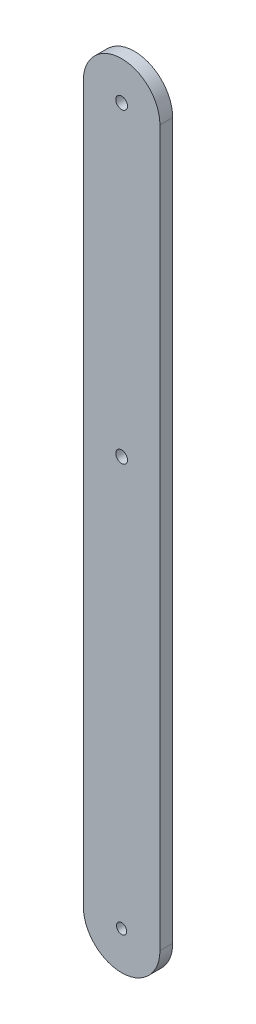
SolidWorks part; units mm, degrees
ref_plane "Front Plane" through (0, 0, 0) normal (0, 0, 1) x (1, 0, 0)
ref_plane "Top Plane" through (0, 0, 0) normal (0, 1, 0) x (1, 0, 0)
ref_plane "Right Plane" through (0, 0, 0) normal (1, 0, 0) x (0, 0, -1)
sketch "Sketch1" plane through (0, 0, 0) normal (0, 0, 1) x (1, 0, 0)
  line L0 (-19.353, -25.4) -> (-19.353, 152.4)
  line L2 (-0.303, 152.4) -> (-0.303, -25.4)
  line L3 (-9.828, 152.4) -> (-9.828, 76.2) construction
  arc A0 (-19.353, 152.4) -> (-0.303, 152.4) centre (-9.828, 152.4) cw
  arc A1 (-19.353, -25.4) -> (-0.303, -25.4) centre (-9.828, -25.4) ccw
  circle A2 centre (-9.828, -25.4) radius 1.27
  circle A3 centre (-9.828, 152.4) radius 1.4605
  circle A4 centre (-9.828, 76.2) radius 1.4605
  dimension "D2" = 2.921
  dimension "D3" = 2.54
  dimension "D4" = 19.05
  dimension "D1" = 177.8
extrude "Boss-Extrude1" add sketch "Sketch1" along normal blind 3.175
